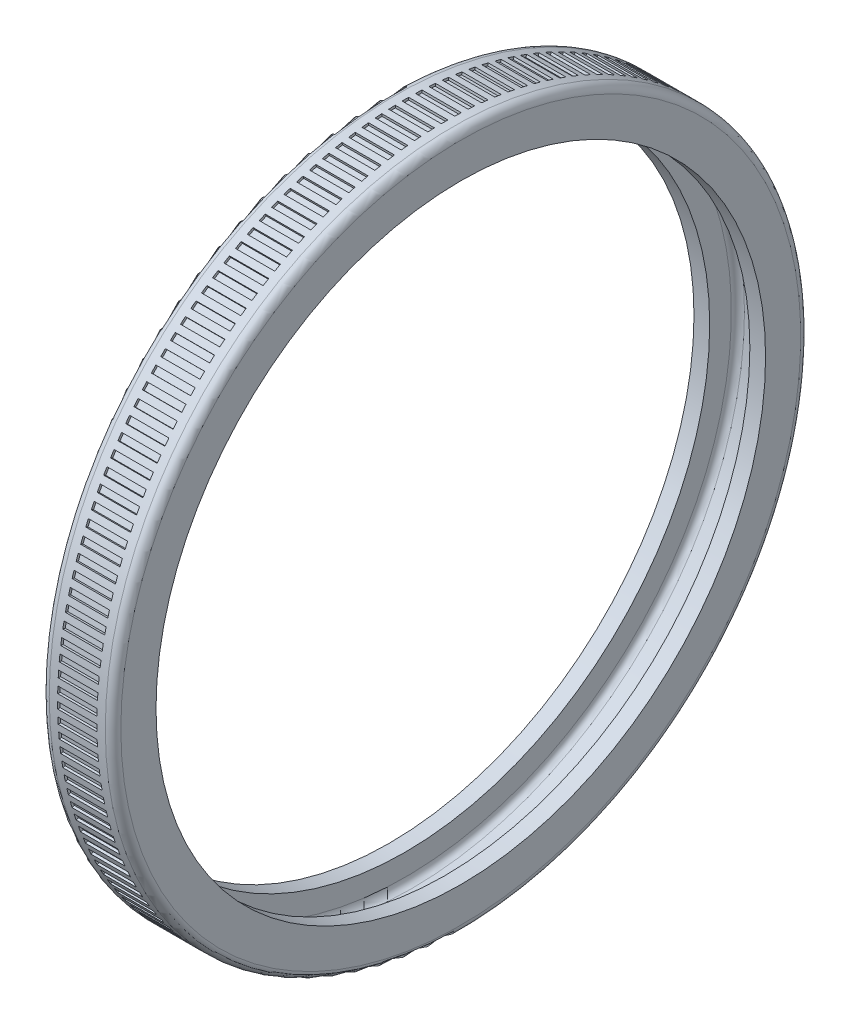
SolidWorks part; units mm, degrees
material "Rubber"
ref_plane "Front" through (0, 0, 0) normal (0, 0, 1) x (1, 0, 0)
ref_plane "Top" through (0, 0, 0) normal (0, 1, 0) x (1, 0, 0)
ref_plane "Right" through (0, 0, 0) normal (1, 0, 0) x (0, 0, -1)
sketch "Sketch1" plane through (0, 0, 0) normal (0, 0, 1) x (1, 0, 0)
  line L0 (-1000, 0) -> (49000, 0) construction
  line L1 (-4.375, 37.25) -> (-4.375, 41.55)
  line L2 (-3.425, 42.5) -> (3.425, 42.5)
  line L3 (4.375, 41.55) -> (4.375, 37.25)
  line L4 (4.375, 37.25) -> (2.4543, 37.25)
  line L5 (-4.375, 37.25) -> (-2.4543, 37.25)
  line L6 (-2.4543, 37.25) -> (-2.4543, 39.9)
  line L7 (-1.6543, 40.7) -> (1.6543, 40.7)
  line L8 (2.4543, 39.9) -> (2.4543, 37.25)
  arc A0 (-4.375, 41.55) -> (-3.425, 42.5) centre (-3.425, 41.55) cw
  arc A1 (3.425, 42.5) -> (4.375, 41.55) centre (3.425, 41.55) cw
  arc A2 (-2.4543, 39.9) -> (-1.6543, 40.7) centre (-1.6543, 39.9) cw
  arc A3 (1.6543, 40.7) -> (2.4543, 39.9) centre (1.6543, 39.9) cw
  point P10 (0, 42.5)
  dimension "D3" = 0.95
  dimension "D6" = 0.8
  dimension "D1" = 85
  dimension "D2" = 8.75
  dimension "D4" = 5.25
  dimension "D5" = 4.9087
  dimension "D7" = 1.8
revolve "Revolve1" add sketch "Sketch1" angle 360 about L0
sketch "Sketch2" plane through (0, 0, 0) normal (1, 0, 0) x (0, 0, -1)
  line L1 (-0.4, 44.2) -> (0.4, 44.2)
  line L2 (-0.4, 44.2) -> (-0.4, 42.2)
  line L3 (-0.4, 42.2) -> (0.4, 42.2)
  line L4 (0.4, 44.2) -> (0.4, 42.2)
  line L5 (-0.4, 44.2) -> (0.4, 42.2) construction
  line L6 (-0.4, 42.2) -> (0.4, 44.2) construction
  circle A0 centre (0, 0) radius 42.5 construction
  point P0 (0, 43.2)
  point P5 (0, 42.5)
  dimension "D1" = 0.3
  dimension "D2" = 0.8
  dimension "D3" = 2
extrude "Cut-Extrude1" cut sketch "Sketch2" against normal mid plane 4.8
pattern_circular "CirPattern1" count 163 over 360 about axis through (0, 0, 0) along (1, 0, 0) of "Cut-Extrude1"
